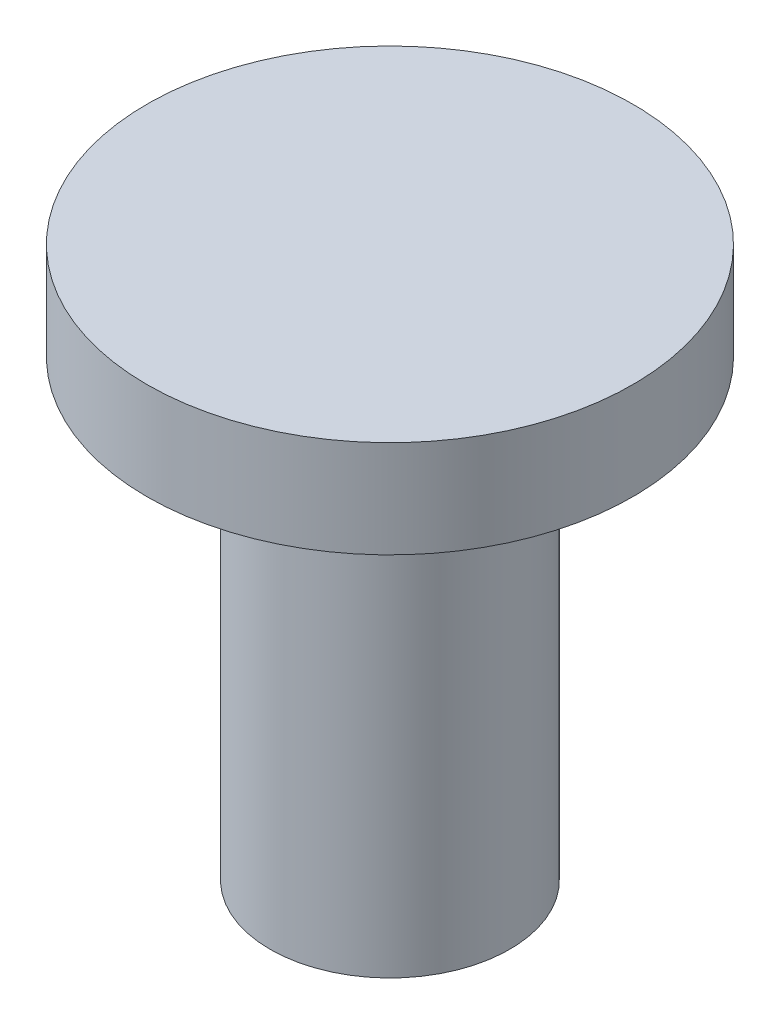
SolidWorks part; units mm, degrees
ref_plane "Front Plane" through (0, 0, 0) normal (0, 0, 1) x (1, 0, 0)
ref_plane "Top Plane" through (0, 0, 0) normal (0, 1, 0) x (1, 0, 0)
ref_plane "Right Plane" through (0, 0, 0) normal (1, 0, 0) x (0, 0, -1)
sketch "Sketch2" plane through (0, 0, 0) normal (1, 0, 0) x (0, 0, -1)
  line L0 (2.0525, 9.4227) -> (-5.4475, 9.4227)
  line L1 (-5.4475, 9.4227) -> (-5.4475, 6.4227)
  line L2 (-5.4475, 6.4227) -> (-1.6475, 6.4227)
  line L3 (-1.6475, 6.4227) -> (-1.6475, -7.5773)
  line L4 (-1.6475, -7.5773) -> (2.0525, -7.5773)
  line L5 (2.0525, 9.4227) -> (2.0525, -7.5773) construction
  line L6 (2.0525, 9.4227) -> (2.0525, -7.5773)
  dimension "D1" = 7.5
  dimension "D2" = 3
  dimension "D3" = 3.8
  dimension "D4" = 14
revolve "Revolve1" add sketch "Sketch2" angle 360 about L5
